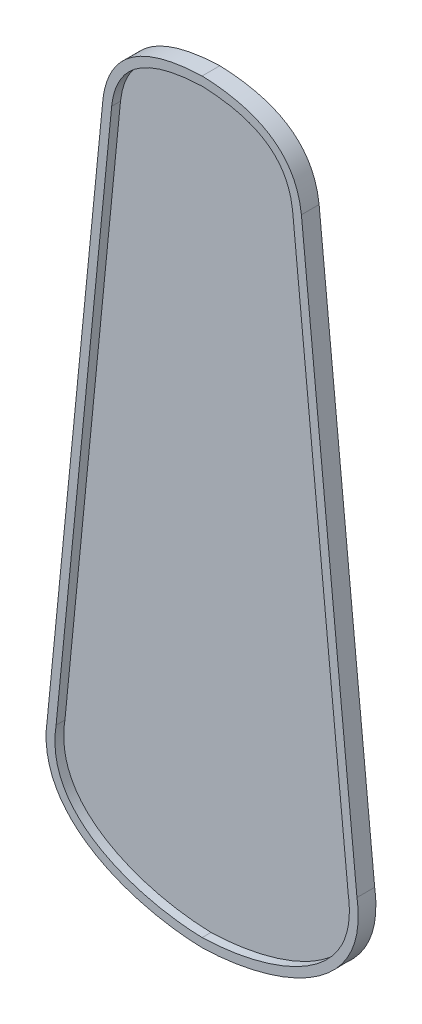
SolidWorks part; units mm, degrees
ref_plane "Front Plane" through (0, 0, 0) normal (0, 0, 1) x (1, 0, 0)
ref_plane "Top Plane" through (0, 0, 0) normal (0, 1, 0) x (1, 0, 0)
ref_plane "Right Plane" through (0, 0, 0) normal (1, 0, 0) x (0, 0, -1)
sketch "Sketch2" plane through (0, 0, 0) normal (0, 0, 1) x (1, 0, 0)
  line L0 (0, 0) -> (0, 812.8) construction
  line L1 (-166.6875, 130.175) -> (166.6875, 130.175) construction
  line L2 (-144.4625, 355.6) -> (144.4625, 355.6) construction
  line L3 (-76.2, 631.825) -> (76.2, 631.825) construction
  line L4 (-38.6922, 736.6) -> (38.6922, 736.6) construction
  line L5 (-76.2, 431.8) -> (76.2, 431.8) construction
  line L6 (-166.6875, 130.175) -> (-106.8761, 736.8337)
  line L7 (166.6875, 130.175) -> (106.8761, 736.8337)
  spline S0 degree 3 poles (0, 0) (-73.6666, 1.7407) (-181.1881, 36.2008) (-166.6875, 130.175) knots 0 0 0 0 1 1 1 1
  spline S1 degree 2 poles (-106.8761, 736.8337) (-98.6556, 809.3851) (0, 812.8) knots 0 0 0 1 1 1
  spline S2 degree 3 poles (0, 0) (73.6666, 1.7407) (181.1881, 36.2008) (166.6875, 130.175) knots 0 0 0 0 1 1 1 1
  spline S3 degree 2 poles (106.8761, 736.8337) (98.6556, 809.3851) (0, 812.8) knots 0 0 0 1 1 1
  point P5 (0, 130.175)
  point P8 (0, 355.6)
  point P11 (0, 631.825)
  point P14 (0, 736.6)
  point P19 (0, 431.8)
  dimension "D9" = 609.6
  dimension "D1" = 812.8
  dimension "D2" = 333.375
  dimension "D3" = 130.175
  dimension "D4" = 355.6
  dimension "D5" = 288.925
  dimension "D6" = 631.825
  dimension "D7" = 152.4
  dimension "D8" = 76.2
  dimension "D10" = 431.8
extrude "Boss-Extrude1" add sketch "Sketch2" along normal blind 19.05
sketch "Sketch4" plane through (0, 0, 19.05) normal (0, 0, 1) x (1, 0, 0)
  line L4 (-97.404, 735.8286) -> (-157.2341, 128.9805)
  line L5 (157.2341, 128.9805) -> (97.404, 735.8286)
  line L6 (-97.404, 735.8286) -> (-157.2341, 128.9805)
  line L7 (157.2341, 128.9805) -> (97.404, 735.8286)
  spline S5 degree 3 poles (-1407.3724, 3705.7609) (-588.1443, 365.5117) (-254.4825, -10.9512) (18.6826, 10.6267) (23.3184, 11.1143) (32.5521, 12.3209) (37.1499, 13.0401) (46.307, 14.7144) (50.8661, 15.6695) (59.9432, 17.8317) (64.4612, 19.0385) (71.2037, 21.0587) (73.4473, 21.7679) (77.899, 23.2533) (80.1096, 24.0303) (86.6934, 26.4698) (91.0187, 28.2403) (99.5226, 32.1119) (103.7013, 34.2127) (108.8153, 37.0856) (109.8326, 37.6725) (111.8556, 38.8726) (112.8623, 39.4865) (115.852, 41.3616) (117.8067, 42.6577) (123.5465, 46.6953) (127.2082, 49.5849) (132.4039, 54.2752) (134.0862, 55.8982) (136.5268, 58.4321) (137.3265, 59.2933) (138.8966, 61.0509) (139.6686, 61.9493) (143.4225, 66.4996) (146.0993, 70.3378) (149.5754, 76.4221) (150.6441, 78.5048) (152.1049, 81.7151) (152.5682, 82.7996) (153.4459, 84.9981) (153.8583, 86.107) (155.7791, 91.6707) (156.8763, 96.211) (157.9179, 103.1446) (158.1642, 105.4763) (158.3888, 109.0033) (158.4395, 110.1861) (158.4933, 112.5484) (158.4966, 113.7281) (158.439, 117.2627) (158.3107, 119.6135) (157.996, 123.1318) (157.8707, 124.3033) (146.0815, 219.5712) (-7.4958, 304.6301) (4112.9689, 661.8727) knots -3.542299 -3.542299 -3.542299 -3.542299 0.0625 0.0625 0.125 0.125 0.1875 0.1875 0.25 0.25 0.3125 0.3125 0.34375 0.34375 0.375 0.375 0.4375 0.4375 0.5 0.5 0.515625 0.515625 0.53125 0.53125 0.5625 0.5625 0.625 0.625 0.65625 0.65625 0.671875 0.671875 0.6875 0.6875 0.75 0.75 0.78125 0.78125 0.796875 0.796875 0.8125 0.8125 0.875 0.875 0.90625 0.90625 0.921875 0.921875 0.9375 0.9375 0.96875 0.96875 0.984375 0.984375 2.240773 2.240773 2.240773 2.240773 only from (0, 9.5278) to (157.2341, 128.9805)
  spline S6 degree 3 poles (-4148.5553, 324.7562) (-75.4972, 249.5672) (-148.8913, 188.5082) (-157.5761, 126.6442) (-157.6533, 126.0601) (-157.8702, 124.3077) (-157.9952, 123.1394) (-158.3091, 119.6343) (-158.437, 117.2972) (-158.5554, 110.2851) (-158.2821, 105.6092) (-157.4113, 99.7625) (-157.21, 98.5912) (-156.7573, 96.2739) (-156.0017, 92.8272) (-155.017, 89.4682) (-152.743, 82.8669) (-150.8208, 78.6215) (-147.9131, 73.5081) (-147.3063, 72.495) (-146.0423, 70.4883) (-145.3898, 69.5021) (-143.3744, 66.5939) (-141.9535, 64.7217) (-137.4778, 59.2882) (-134.2112, 55.9092) (-129.8247, 51.9463) (-128.9329, 51.1676) (-127.1321, 49.6453) (-126.2216, 48.9004) (-123.4616, 46.7115) (-121.5837, 45.3133) (-115.8481, 41.2826) (-111.8891, 38.8133) (-103.7461, 34.2369) (-99.562, 32.1301) (-94.2098, 29.6931) (-93.1322, 29.215) (-90.9715, 28.2809) (-89.8883, 27.8247) (-86.6311, 26.4875) (-84.4492, 25.6377) (-77.8744, 23.2033) (-73.4528, 21.7334) (-64.542, 19.0618) (-60.0528, 17.8603) (-51.013, 15.7021) (-46.4622, 14.7455) (-37.3022, 13.0652) (-32.6929, 12.3414) (-25.7353, 11.4291) (-23.4089, 11.154) (-18.7411, 10.6628) (-16.4019, 10.4469) (268.8258, -12.1212) (579.7971, 410.5336) (1078.5145, 3808.3979) knots -0.811833 -0.811833 -0.811833 -0.811833 0.007812 0.007812 0.015625 0.015625 0.03125 0.03125 0.0625 0.0625 0.125 0.125 0.140625 0.140625 0.15625 0.1875 0.1875 0.25 0.25 0.265625 0.265625 0.28125 0.28125 0.3125 0.3125 0.375 0.375 0.390625 0.390625 0.40625 0.40625 0.4375 0.4375 0.5 0.5 0.5625 0.5625 0.578125 0.578125 0.59375 0.59375 0.625 0.625 0.6875 0.6875 0.75 0.75 0.8125 0.8125 0.875 0.875 0.90625 0.90625 0.9375 0.9375 4.715825 4.715825 4.715825 4.715825 only from (-157.2341, 128.9805) to (0, 9.5278)
  spline S7 degree 3 poles (4026.8071, 1198.47) (-476.9525, 185.115) (135.5309, 552.4903) (95.5701, 746.6077) (94.8936, 749.2437) (93.2479, 754.4366) (92.2787, 756.9936) (90.8531, 760.132) (90.5571, 760.7568) (89.9476, 761.9913) (89.6335, 762.6021) (88.6631, 764.4149) (87.9786, 765.5975) (85.811, 769.0663) (84.2136, 771.2733) (81.5841, 774.4224) (80.6688, 775.4452) (79.237, 776.9387) (78.7497, 777.4298) (77.7631, 778.3916) (77.2629, 778.8631) (72.7002, 783.0248) (68.2159, 786.1463) (62.1872, 789.477) (60.9642, 790.112) (58.502, 791.3173) (57.2604, 791.889) (53.5069, 793.5192) (50.9664, 794.4935) (43.2487, 797.1317) (37.9761, 798.514) (31.2662, 799.8903) (29.9175, 800.1478) (27.2187, 800.6279) (25.8675, 800.8507) (21.8086, 801.471) (19.0959, 801.8208) (-244.595, 830.3753) (-559.8551, 351.1711) (-356.9349, 4715.738) knots -4.418652 -4.418652 -4.418652 -4.418652 0.0625 0.0625 0.125 0.125 0.1875 0.1875 0.203125 0.203125 0.21875 0.21875 0.25 0.25 0.3125 0.3125 0.34375 0.34375 0.359375 0.359375 0.375 0.375 0.5 0.5 0.53125 0.53125 0.5625 0.5625 0.625 0.625 0.75 0.75 0.78125 0.78125 0.8125 0.8125 0.875 0.875 6.874627 6.874627 6.874627 6.874627 only from (97.404, 735.8286) to (0, 803.2691)
  spline S8 degree 3 poles (147.4424, 4724.4888) (603.5502, 334.2115) (250.0916, 830.8943) (-21.7277, 801.5373) (-27.0989, 800.738) (-35.0848, 799.1104) (-37.7348, 798.496) (-43.0068, 797.0975) (-45.6288, 796.3136) (-49.5363, 794.9844) (-50.8325, 794.5164) (-53.3956, 793.5319) (-54.6646, 793.0148) (-58.4315, 791.3834) (-60.8893, 790.1892) (-65.6799, 787.5521) (-68.0128, 786.1093) (-72.5306, 782.9287) (-74.6722, 781.2203) (-78.6966, 777.5609) (-80.5811, 775.6087) (-83.2058, 772.4869) (-84.0471, 771.414) (-85.6608, 769.2022) (-86.4338, 768.0622) (-90.1161, 762.2045) (-92.3538, 757.2181) (-94.4402, 750.6837) (-94.8218, 749.3617) (-95.5171, 746.6889) (-95.8291, 745.3446) (-133.2254, 564.319) (414.1515, 278.1795) (-4057.3505, 906.2099) knots -6.034072 -6.034072 -6.034072 -6.034072 0.125 0.125 0.25 0.25 0.3125 0.3125 0.375 0.375 0.40625 0.40625 0.4375 0.4375 0.5 0.5 0.5625 0.5625 0.625 0.625 0.6875 0.6875 0.71875 0.71875 0.75 0.75 0.875 0.875 0.90625 0.90625 0.9375 0.9375 5.097806 5.097806 5.097806 5.097806 only from (0, 803.2691) to (-97.404, 735.8286)
  spline S9 degree 3 poles (0, 9.5278) (4.6968, 9.643) (9.3718, 9.8912) (18.6826, 10.6267) (23.3184, 11.1143) (32.5521, 12.3209) (37.1499, 13.0401) (46.307, 14.7144) (50.8661, 15.6695) (59.9432, 17.8317) (64.4612, 19.0385) (71.2037, 21.0587) (73.4473, 21.7679) (77.899, 23.2533) (80.1096, 24.0303) (86.6934, 26.4698) (91.0187, 28.2403) (99.5226, 32.1119) (103.7013, 34.2127) (108.8153, 37.0856) (109.8326, 37.6725) (111.8556, 38.8726) (112.8623, 39.4865) (115.852, 41.3616) (117.8067, 42.6577) (123.5465, 46.6953) (127.2082, 49.5849) (132.4039, 54.2752) (134.0862, 55.8982) (136.5268, 58.4321) (137.3265, 59.2933) (138.8966, 61.0509) (139.6686, 61.9493) (143.4225, 66.4996) (146.0993, 70.3378) (149.5754, 76.4221) (150.6441, 78.5048) (152.1049, 81.7151) (152.5682, 82.7996) (153.4459, 84.9981) (153.8583, 86.107) (155.7791, 91.6707) (156.8763, 96.211) (157.9179, 103.1446) (158.1642, 105.4763) (158.3888, 109.0033) (158.4395, 110.1861) (158.4933, 112.5484) (158.4966, 113.7281) (158.439, 117.2627) (158.3107, 119.6135) (157.996, 123.1318) (157.8707, 124.3033) (157.5811, 126.6437) (157.4143, 127.8126) (157.2341, 128.9805) knots 0 0 0 0 0.0625 0.0625 0.125 0.125 0.1875 0.1875 0.25 0.25 0.3125 0.3125 0.34375 0.34375 0.375 0.375 0.4375 0.4375 0.5 0.5 0.515625 0.515625 0.53125 0.53125 0.5625 0.5625 0.625 0.625 0.65625 0.65625 0.671875 0.671875 0.6875 0.6875 0.75 0.75 0.78125 0.78125 0.796875 0.796875 0.8125 0.8125 0.875 0.875 0.90625 0.90625 0.921875 0.921875 0.9375 0.9375 0.96875 0.96875 0.984375 0.984375 1 1 1 1
  spline S10 degree 3 poles (-157.2341, 128.9805) (-157.3242, 128.3965) (-157.4121, 127.8124) (-157.5761, 126.6442) (-157.6533, 126.0601) (-157.8702, 124.3077) (-157.9952, 123.1394) (-158.3091, 119.6343) (-158.437, 117.2972) (-158.5554, 110.2851) (-158.2821, 105.6092) (-157.4113, 99.7625) (-157.21, 98.5912) (-156.7573, 96.2739) (-156.0017, 92.8272) (-155.017, 89.4682) (-152.743, 82.8669) (-150.8208, 78.6215) (-147.9131, 73.5081) (-147.3063, 72.495) (-146.0423, 70.4883) (-145.3898, 69.5021) (-143.3744, 66.5939) (-141.9535, 64.7217) (-137.4778, 59.2882) (-134.2112, 55.9092) (-129.8247, 51.9463) (-128.9329, 51.1676) (-127.1321, 49.6453) (-126.2216, 48.9004) (-123.4616, 46.7115) (-121.5837, 45.3133) (-115.8481, 41.2826) (-111.8891, 38.8133) (-103.7461, 34.2369) (-99.562, 32.1301) (-94.2098, 29.6931) (-93.1322, 29.215) (-90.9715, 28.2809) (-89.8883, 27.8247) (-86.6311, 26.4875) (-84.4492, 25.6377) (-77.8744, 23.2033) (-73.4528, 21.7334) (-64.542, 19.0618) (-60.0528, 17.8603) (-51.013, 15.7021) (-46.4622, 14.7455) (-37.3022, 13.0652) (-32.6929, 12.3414) (-25.7353, 11.4291) (-23.4089, 11.154) (-18.7411, 10.6628) (-16.4019, 10.4469) (-9.3827, 9.8915) (-4.6955, 9.643) (0, 9.5278) knots 0 0 0 0 0.007812 0.007812 0.015625 0.015625 0.03125 0.03125 0.0625 0.0625 0.125 0.125 0.140625 0.140625 0.15625 0.1875 0.1875 0.25 0.25 0.265625 0.265625 0.28125 0.28125 0.3125 0.3125 0.375 0.375 0.390625 0.390625 0.40625 0.40625 0.4375 0.4375 0.5 0.5 0.5625 0.5625 0.578125 0.578125 0.59375 0.59375 0.625 0.625 0.6875 0.6875 0.75 0.75 0.8125 0.8125 0.875 0.875 0.90625 0.90625 0.9375 0.9375 1 1 1 1
  spline S11 degree 3 poles (97.404, 735.8286) (97.0923, 738.563) (96.6694, 741.2674) (95.5701, 746.6077) (94.8936, 749.2437) (93.2479, 754.4366) (92.2787, 756.9936) (90.8531, 760.132) (90.5571, 760.7568) (89.9476, 761.9913) (89.6335, 762.6021) (88.6631, 764.4149) (87.9786, 765.5975) (85.811, 769.0663) (84.2136, 771.2733) (81.5841, 774.4224) (80.6688, 775.4452) (79.237, 776.9387) (78.7497, 777.4298) (77.7631, 778.3916) (77.2629, 778.8631) (72.7002, 783.0248) (68.2159, 786.1463) (62.1872, 789.477) (60.9642, 790.112) (58.502, 791.3173) (57.2604, 791.889) (53.5069, 793.5192) (50.9664, 794.4935) (43.2487, 797.1317) (37.9761, 798.514) (31.2662, 799.8903) (29.9175, 800.1478) (27.2187, 800.6279) (25.8675, 800.8507) (21.8086, 801.471) (19.0959, 801.8208) (10.94, 802.704) (5.4792, 803.0725) (0, 803.2691) knots 0 0 0 0 0.0625 0.0625 0.125 0.125 0.1875 0.1875 0.203125 0.203125 0.21875 0.21875 0.25 0.25 0.3125 0.3125 0.34375 0.34375 0.359375 0.359375 0.375 0.375 0.5 0.5 0.53125 0.53125 0.5625 0.5625 0.625 0.625 0.75 0.75 0.78125 0.78125 0.8125 0.8125 0.875 0.875 1 1 1 1
  spline S12 degree 3 poles (0, 803.2691) (-5.4711, 803.0728) (-10.9139, 802.7052) (-21.7277, 801.5373) (-27.0989, 800.738) (-35.0848, 799.1104) (-37.7348, 798.496) (-43.0068, 797.0975) (-45.6288, 796.3136) (-49.5363, 794.9844) (-50.8325, 794.5164) (-53.3956, 793.5319) (-54.6646, 793.0148) (-58.4315, 791.3834) (-60.8893, 790.1892) (-65.6799, 787.5521) (-68.0128, 786.1093) (-72.5306, 782.9287) (-74.6722, 781.2203) (-78.6966, 777.5609) (-80.5811, 775.6087) (-83.2058, 772.4869) (-84.0471, 771.414) (-85.6608, 769.2022) (-86.4338, 768.0622) (-90.1161, 762.2045) (-92.3538, 757.2181) (-94.4402, 750.6837) (-94.8218, 749.3617) (-95.5171, 746.6889) (-95.8291, 745.3446) (-96.6655, 741.2957) (-97.0912, 738.5724) (-97.404, 735.8286) knots 0 0 0 0 0.125 0.125 0.25 0.25 0.3125 0.3125 0.375 0.375 0.40625 0.40625 0.4375 0.4375 0.5 0.5 0.5625 0.5625 0.625 0.625 0.6875 0.6875 0.71875 0.71875 0.75 0.75 0.875 0.875 0.90625 0.90625 0.9375 0.9375 1 1 1 1
  dimension "D1" = 9.525
extrude "Cut-Extrude1" cut sketch "Sketch4" against normal blind 9.525
